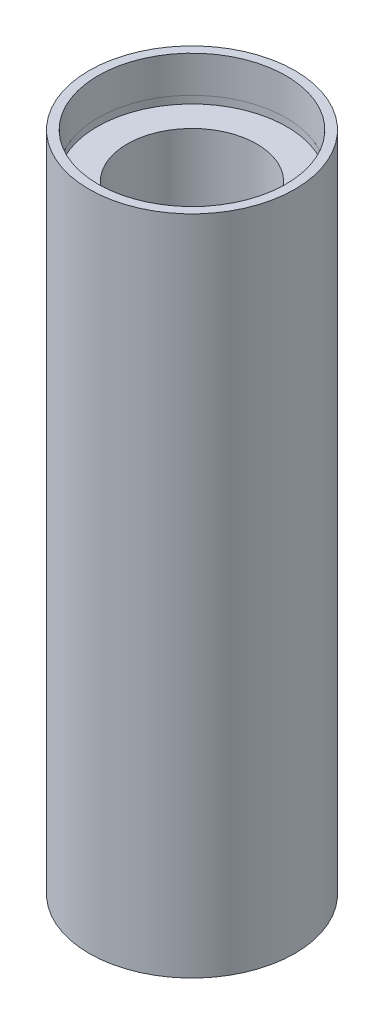
SolidWorks part; units mm, degrees
ref_plane "前视基准面" through (0, 0, 0) normal (0, 0, 1) x (1, 0, 0)
ref_plane "上视基准面" through (0, 0, 0) normal (0, 1, 0) x (1, 0, 0)
ref_plane "右视基准面" through (0, 0, 0) normal (1, 0, 0) x (0, 0, -1)
sketch "草图1" plane through (0, 0, 0) normal (0, 0, 1) x (1, 0, 0)
  line L0 (0, 161.3762) -> (0, 0) construction
  line L1 (141.7365, 0) -> (-131.7984, 0) construction
  line L2 (11.1, 0) -> (11.1, 4.5)
  line L3 (11.7, 4.5) -> (11.7, 5.5)
  line L4 (11.1, 4.5) -> (11.7, 4.5)
  line L5 (8, 5.5) -> (8, 76.2)
  line L6 (11.7, 5.5) -> (8, 5.5)
  line L7 (12.7, 0) -> (12.7, 81.7)
  line L8 (11.1, 0) -> (12.7, 0)
  line L9 (11.6, 81.7) -> (11.6, 77.2)
  line L10 (11.6, 81.7) -> (12.7, 81.7)
  line L11 (11.7, 77.2) -> (11.7, 76.2)
  line L12 (11.6, 77.2) -> (11.7, 77.2)
  line L13 (8, 76.2) -> (11.7, 76.2)
  point P15 (11.6, 79.45)
  dimension "D1" = 11.1
  dimension "D2" = 4.5
  dimension "D3" = 11.7
  dimension "D4" = 8
  dimension "D5" = 12.7
  dimension "D6" = 11.6
  dimension "D7" = 4.5
  dimension "D8" = 11.7
  dimension "D9" = 5.5
  dimension "D10" = 1
  dimension "D11" = 76.2
revolve "旋转1" add sketch "草图1" angle 360 about L0
cosmetic thread "装饰螺纹线1" parameters "D2"=23.2
cosmetic thread "装饰螺纹线2" parameters "D2"=17
cosmetic thread "装饰螺纹线3" parameters "D2"=23.21
